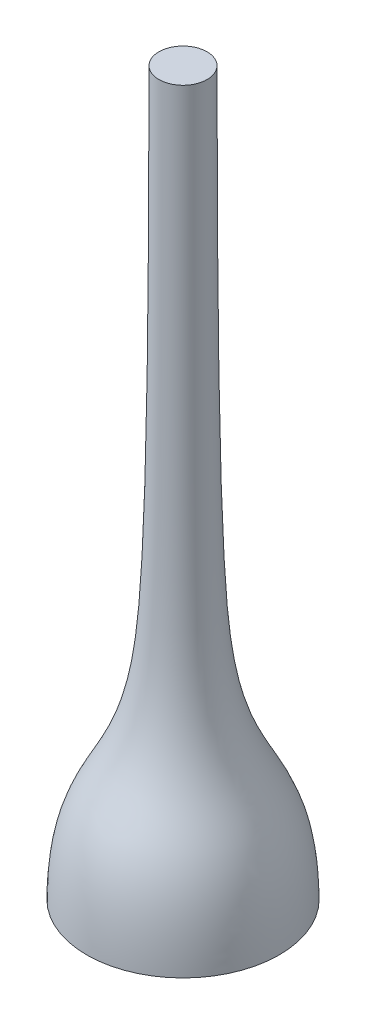
SolidWorks part; units mm, degrees
ref_plane "Front Plane" through (0, 0, 0) normal (0, 0, 1) x (1, 0, 0)
ref_plane "Top Plane" through (0, 0, 0) normal (0, 1, 0) x (1, 0, 0)
ref_plane "Right Plane" through (0, 0, 0) normal (1, 0, 0) x (0, 0, -1)
sketch "Sketch1" plane through (0, 0, 0) normal (0, 0, 1) x (1, 0, 0)
  line L0 (0, 15) -> (0, 0)
  line L1 (0, 0) -> (2, 0)
  line L2 (0, 15) -> (0.5, 15)
  spline S0 degree 3 poles (0.5, 15) (0.5017, 9.6608) (0.5714, 5.9949) (0.942, 2.0336) (1.97, 2.3515) (2, 0) knots 0 0 0 0 0.230232 0.330232 1 1 1 1
  dimension "D1" = 15
  dimension "D2" = 2
  dimension "D3" = 0.5
revolve "Revolve8" add sketch "Sketch1" angle 360 about L0
